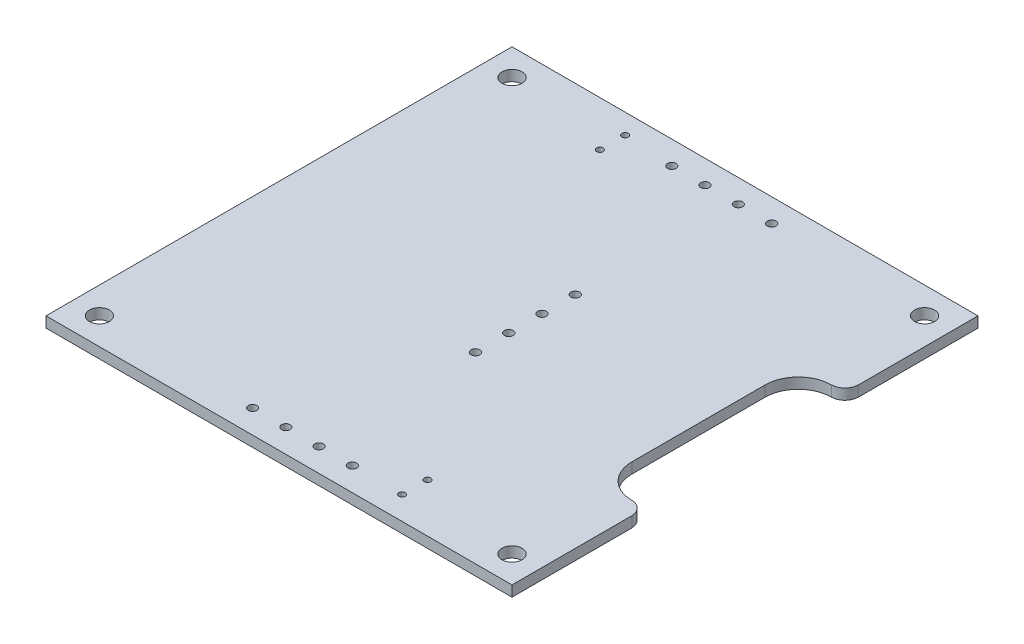
SolidWorks part; units mm, degrees
ref_plane "Front Plane" through (0, 0, 0) normal (0, 0, 1) x (1, 0, 0)
ref_plane "Top Plane" through (0, 0, 0) normal (0, 1, 0) x (1, 0, 0)
ref_plane "Right Plane" through (0, 0, 0) normal (1, 0, 0) x (0, 0, -1)
sketch "Sketch1" plane through (0, 0, 0) normal (0, 1, 0) x (1, 0, 0)
  line L0 (-16.002, 25.9927) -> (-28.0035, 25.9927) construction
  line L1 (-28.0035, 33.9937) -> (-16.002, 33.9937) construction
  line L2 (-16.002, 33.9937) -> (-16.002, 25.9927) construction
  line L3 (15.494, -33.5068) -> (27.4955, -33.5068) construction
  line L4 (27.4955, -33.5068) -> (27.4955, -25.5058) construction
  line L5 (15.494, -25.5058) -> (15.494, -33.5068) construction
  line L6 (-4.4662, 10.8585) -> (8.4667, 10.8585) construction
  line L7 (8.4667, -10.3293) -> (-4.4662, -10.3293) construction
  line L8 (-10.8585, -25.019) -> (-10.8585, -37.973) construction
  line L9 (10.3293, -37.973) -> (10.3293, -25.019) construction
  line L10 (10.8585, 25.019) -> (10.8585, 37.973) construction
  line L11 (10.8585, 37.973) -> (-10.3293, 37.973) construction
  line L12 (-10.3293, 37.973) -> (-10.3293, 25.019) construction
  line L13 (-10.3293, 25.019) -> (10.8585, 25.019) construction
  line L14 (35.0097, 35.0097) -> (-35.0097, 35.0097)
  line L15 (-35.0097, -35.0097) -> (35.0097, -35.0097)
  line L16 (35.0097, -35.0097) -> (35.0097, -16.9968)
  line L17 (35.0097, -16.9968) -> (34.9885, -16.9968)
  line L18 (32.9988, -15.0072) -> (32.9777, -14.986)
  line L19 (28.0035, -9.9907) -> (28.0035, 9.9907)
  line L20 (28.0035, 9.9907) -> (28.0035, 10.0118)
  line L21 (32.9777, 15.0072) -> (32.9988, 15.0283)
  line L22 (34.9885, 17.018) -> (35.0097, 16.9968)
  line L23 (-35.0097, 35.0097) -> (-35.0097, -35.0097)
  line L24 (-4.4662, -10.3293) -> (-4.4662, 10.8585) construction
  line L25 (-10.8585, -25.019) -> (10.3293, -25.019) construction
  line L26 (10.3293, -37.973) -> (-10.8585, -37.973) construction
  line L27 (15.494, -25.5058) -> (27.4955, -25.5058) construction
  line L28 (35.0097, -35.0097) -> (-35.0097, 35.0097) construction
  line L29 (35.0097, 35.0097) -> (-35.0097, -35.0097) construction
  line L30 (-28.0035, 33.9937) -> (-28.0035, 25.9927) construction
  line L31 (-33.9937, 31.0092) -> (-28.0247, 31.0092) construction
  line L32 (-19.304, 30.1202) -> (-10.7103, 30.1202) construction
  line L33 (-8.1492, 31.5172) -> (-6.858, 31.5172) construction
  line L34 (-3.1538, 31.5172) -> (-1.8627, 31.5172) construction
  line L35 (1.8415, 31.5172) -> (3.1327, 31.5172) construction
  line L36 (6.8368, 31.5172) -> (8.1492, 31.5172) construction
  line L37 (28.0035, 31.0092) -> (33.9725, 31.0092) construction
  line L38 (1.3335, 7.5142) -> (2.6458, 7.5142) construction
  line L39 (1.3335, 2.5188) -> (2.6458, 2.5188) construction
  line L40 (1.3335, -2.4765) -> (2.6458, -2.4765) construction
  line L41 (1.3335, -7.493) -> (2.6458, -7.493) construction
  line L42 (-33.9937, -30.988) -> (-28.0247, -30.988) construction
  line L43 (-8.1492, -31.4748) -> (-6.858, -31.4748) construction
  line L44 (-3.1538, -31.4748) -> (-1.8627, -31.4748) construction
  line L45 (1.8415, -31.4748) -> (3.1327, -31.4748) construction
  line L46 (6.8368, -31.4748) -> (8.1492, -31.4748) construction
  line L47 (10.7103, -29.591) -> (19.2828, -29.591) construction
  line L48 (28.0035, -30.988) -> (33.9725, -30.988) construction
  line L49 (-15.494, 32.004) -> (-14.5203, 32.004) construction
  line L50 (-15.494, 28.2152) -> (-14.5203, 28.2152) construction
  line L51 (14.4992, -27.686) -> (15.4728, -27.686) construction
  line L52 (14.4992, -31.496) -> (15.4728, -31.496) construction
  circle A0 centre (-7.5036, 31.5172) radius 0.6456
  circle A1 centre (-2.5083, 31.5172) radius 0.6456
  circle A2 centre (2.4871, 31.5172) radius 0.6456
  circle A3 centre (7.493, 31.5172) radius 0.6562
  circle A4 centre (-15.0072, 28.2152) radius 0.4868
  circle A5 centre (-15.0072, 32.004) radius 0.4868
  circle A6 centre (1.9897, 7.5142) radius 0.6562
  circle A7 centre (1.9897, 2.5188) radius 0.6562
  circle A8 centre (1.9897, -2.4765) radius 0.6562
  circle A9 centre (1.9897, -7.493) radius 0.6562
  circle A10 centre (-7.5036, -31.4748) radius 0.6456
  circle A11 centre (-2.5083, -31.4748) radius 0.6456
  circle A12 centre (2.4871, -31.4748) radius 0.6456
  circle A13 centre (7.493, -31.4748) radius 0.6562
  circle A14 centre (-31.0092, 31.0092) radius 1.5
  circle A15 centre (30.988, 31.0092) radius 1.5
  circle A16 centre (-31.0092, -30.988) radius 1.5
  circle A17 centre (30.988, -30.988) radius 1.5
  circle A18 centre (14.986, -27.686) radius 0.4868
  circle A19 centre (14.986, -31.496) radius 0.4868
  spline S2 degree 3 poles (14.4992, -31.496) (14.4992, -31.75) (14.7108, -31.9828) (14.986, -31.9828) (15.24, -31.9828) (15.4728, -31.75) (15.4728, -31.496) knots 2 2 2 2 3 3 3 4 4 4 4 construction
  spline S3 degree 3 poles (15.4728, -31.496) (15.4728, -31.2208) (15.24, -31.0092) (14.986, -31.0092) (14.7108, -31.0092) (14.4992, -31.2208) (14.4992, -31.496) knots 0 0 0 0 1 1 1 2 2 2 2 construction
  spline S4 degree 3 poles (14.4992, -27.686) (14.4992, -27.94) (14.7108, -28.1728) (14.986, -28.1728) (15.24, -28.1728) (15.4728, -27.94) (15.4728, -27.686) knots 2 2 2 2 3 3 3 4 4 4 4 construction
  spline S5 degree 3 poles (15.4728, -27.686) (15.4728, -27.4108) (15.24, -27.1992) (14.986, -27.1992) (14.7108, -27.1992) (14.4992, -27.4108) (14.4992, -27.686) knots 0 0 0 0 1 1 1 2 2 2 2 construction
  spline S6 degree 3 poles (10.7103, -29.591) (10.7103, -31.9617) (12.6153, -33.8878) (14.986, -33.8878) (17.3567, -33.8878) (19.2828, -31.9617) (19.2828, -29.591) knots 2 2 2 2 3 3 3 4 4 4 4 construction
  spline S7 degree 3 poles (19.2828, -29.591) (19.2828, -27.1992) (17.3567, -25.2942) (14.986, -25.2942) (12.6153, -25.2942) (10.7103, -27.1992) (10.7103, -29.591) knots 0 0 0 0 1 1 1 2 2 2 2 construction
  spline S8 degree 3 poles (-15.494, 32.004) (-15.494, 31.75) (-15.2823, 31.5172) (-15.0072, 31.5172) (-14.7532, 31.5172) (-14.5203, 31.75) (-14.5203, 32.004) knots 2 2 2 2 3 3 3 4 4 4 4 construction
  spline S9 degree 3 poles (-14.5203, 32.004) (-14.5203, 32.2792) (-14.7532, 32.4908) (-15.0072, 32.4908) (-15.2823, 32.4908) (-15.494, 32.2792) (-15.494, 32.004) knots 0 0 0 0 1 1 1 2 2 2 2 construction
  spline S10 degree 3 poles (-15.494, 28.2152) (-15.494, 27.9612) (-15.2823, 27.7283) (-15.0072, 27.7283) (-14.7532, 27.7283) (-14.5203, 27.9612) (-14.5203, 28.2152) knots 2 2 2 2 3 3 3 4 4 4 4 construction
  spline S11 degree 3 poles (-14.5203, 28.2152) (-14.5203, 28.4903) (-14.7532, 28.702) (-15.0072, 28.702) (-15.2823, 28.702) (-15.494, 28.4903) (-15.494, 28.2152) knots 0 0 0 0 1 1 1 2 2 2 2 construction
  spline S12 degree 3 poles (-19.304, 30.1202) (-19.304, 27.7495) (-17.399, 25.8233) (-15.0072, 25.8233) (-12.6365, 25.8233) (-10.7103, 27.7495) (-10.7103, 30.1202) knots 2 2 2 2 3 3 3 4 4 4 4 construction
  spline S13 degree 3 poles (-10.7103, 30.1202) (-10.7103, 32.4908) (-12.6365, 34.3958) (-15.0072, 34.3958) (-17.399, 34.3958) (-19.304, 32.4908) (-19.304, 30.1202) knots 0 0 0 0 1 1 1 2 2 2 2 construction
  spline S14 degree 3 poles (1.3335, -7.493) (1.3335, -7.8528) (1.6087, -8.1492) (1.9897, -8.1492) (2.3495, -8.1492) (2.6458, -7.8528) (2.6458, -7.493) knots 2 2 2 2 3 3 3 4 4 4 4 construction
  spline S15 degree 3 poles (2.6458, -7.493) (2.6458, -7.112) (2.3495, -6.8368) (1.9897, -6.8368) (1.6087, -6.8368) (1.3335, -7.112) (1.3335, -7.493) knots 0 0 0 0 1 1 1 2 2 2 2 construction
  spline S16 degree 3 poles (1.3335, -2.4765) (1.3335, -2.8363) (1.6087, -3.1327) (1.9897, -3.1327) (2.3495, -3.1327) (2.6458, -2.8363) (2.6458, -2.4765) knots 2 2 2 2 3 3 3 4 4 4 4 construction
  spline S17 degree 3 poles (2.6458, -2.4765) (2.6458, -2.1167) (2.3495, -1.8415) (1.9897, -1.8415) (1.6087, -1.8415) (1.3335, -2.1167) (1.3335, -2.4765) knots 0 0 0 0 1 1 1 2 2 2 2 construction
  spline S18 degree 3 poles (1.3335, 7.5142) (1.3335, 7.1543) (1.6087, 6.858) (1.9897, 6.858) (2.3495, 6.858) (2.6458, 7.1543) (2.6458, 7.5142) knots 2 2 2 2 3 3 3 4 4 4 4 construction
  spline S19 degree 3 poles (2.6458, 7.5142) (2.6458, 7.874) (2.3495, 8.1492) (1.9897, 8.1492) (1.6087, 8.1492) (1.3335, 7.874) (1.3335, 7.5142) knots 0 0 0 0 1 1 1 2 2 2 2 construction
  spline S20 degree 3 poles (1.3335, 2.5188) (1.3335, 2.159) (1.6087, 1.8627) (1.9897, 1.8627) (2.3495, 1.8627) (2.6458, 2.159) (2.6458, 2.5188) knots 2 2 2 2 3 3 3 4 4 4 4 construction
  spline S21 degree 3 poles (2.6458, 2.5188) (2.6458, 2.8787) (2.3495, 3.1538) (1.9897, 3.1538) (1.6087, 3.1538) (1.3335, 2.8787) (1.3335, 2.5188) knots 0 0 0 0 1 1 1 2 2 2 2 construction
  spline S22 degree 3 poles (6.8368, -31.4748) (6.8368, -31.8347) (7.112, -32.131) (7.493, -32.131) (7.8528, -32.131) (8.1492, -31.8347) (8.1492, -31.4748) knots 2 2 2 2 3 3 3 4 4 4 4 construction
  spline S23 degree 3 poles (8.1492, -31.4748) (8.1492, -31.115) (7.8528, -30.8398) (7.493, -30.8398) (7.112, -30.8398) (6.8368, -31.115) (6.8368, -31.4748) knots 0 0 0 0 1 1 1 2 2 2 2 construction
  spline S24 degree 3 poles (1.8415, -31.4748) (1.8415, -31.8347) (2.1167, -32.131) (2.4765, -32.131) (2.8363, -32.131) (3.1327, -31.8347) (3.1327, -31.4748) knots 2 2 2 2 3 3 3 4 4 4 4 construction
  spline S25 degree 3 poles (3.1327, -31.4748) (3.1327, -31.115) (2.8363, -30.8398) (2.4765, -30.8398) (2.1167, -30.8398) (1.8415, -31.115) (1.8415, -31.4748) knots 0 0 0 0 1 1 1 2 2 2 2 construction
  spline S26 degree 3 poles (-8.1492, -31.4748) (-8.1492, -31.8347) (-7.874, -32.131) (-7.5142, -32.131) (-7.1543, -32.131) (-6.858, -31.8347) (-6.858, -31.4748) knots 2 2 2 2 3 3 3 4 4 4 4 construction
  spline S27 degree 3 poles (-6.858, -31.4748) (-6.858, -31.115) (-7.1543, -30.8398) (-7.5142, -30.8398) (-7.874, -30.8398) (-8.1492, -31.115) (-8.1492, -31.4748) knots 0 0 0 0 1 1 1 2 2 2 2 construction
  spline S28 degree 3 poles (-3.1538, -31.4748) (-3.1538, -31.8347) (-2.8787, -32.131) (-2.5188, -32.131) (-2.159, -32.131) (-1.8627, -31.8347) (-1.8627, -31.4748) knots 2 2 2 2 3 3 3 4 4 4 4 construction
  spline S29 degree 3 poles (-1.8627, -31.4748) (-1.8627, -31.115) (-2.159, -30.8398) (-2.5188, -30.8398) (-2.8787, -30.8398) (-3.1538, -31.115) (-3.1538, -31.4748) knots 0 0 0 0 1 1 1 2 2 2 2 construction
  spline S30 degree 3 poles (-8.1492, 31.5172) (-8.1492, 31.1573) (-7.874, 30.861) (-7.5142, 30.861) (-7.1543, 30.861) (-6.858, 31.1573) (-6.858, 31.5172) knots 2 2 2 2 3 3 3 4 4 4 4 construction
  spline S31 degree 3 poles (-6.858, 31.5172) (-6.858, 31.877) (-7.1543, 32.1522) (-7.5142, 32.1522) (-7.874, 32.1522) (-8.1492, 31.877) (-8.1492, 31.5172) knots 0 0 0 0 1 1 1 2 2 2 2 construction
  spline S32 degree 3 poles (-3.1538, 31.5172) (-3.1538, 31.1573) (-2.8787, 30.861) (-2.5188, 30.861) (-2.159, 30.861) (-1.8627, 31.1573) (-1.8627, 31.5172) knots 2 2 2 2 3 3 3 4 4 4 4 construction
  spline S33 degree 3 poles (-1.8627, 31.5172) (-1.8627, 31.877) (-2.159, 32.1522) (-2.5188, 32.1522) (-2.8787, 32.1522) (-3.1538, 31.877) (-3.1538, 31.5172) knots 0 0 0 0 1 1 1 2 2 2 2 construction
  spline S34 degree 3 poles (6.8368, 31.5172) (6.8368, 31.1573) (7.112, 30.861) (7.493, 30.861) (7.8528, 30.861) (8.1492, 31.1573) (8.1492, 31.5172) knots 2 2 2 2 3 3 3 4 4 4 4 construction
  spline S35 degree 3 poles (8.1492, 31.5172) (8.1492, 31.877) (7.8528, 32.1522) (7.493, 32.1522) (7.112, 32.1522) (6.8368, 31.877) (6.8368, 31.5172) knots 0 0 0 0 1 1 1 2 2 2 2 construction
  spline S36 degree 3 poles (1.8415, 31.5172) (1.8415, 31.1573) (2.1167, 30.861) (2.4765, 30.861) (2.8363, 30.861) (3.1327, 31.1573) (3.1327, 31.5172) knots 2 2 2 2 3 3 3 4 4 4 4 construction
  spline S37 degree 3 poles (3.1327, 31.5172) (3.1327, 31.877) (2.8363, 32.1522) (2.4765, 32.1522) (2.1167, 32.1522) (1.8415, 31.877) (1.8415, 31.5172) knots 0 0 0 0 1 1 1 2 2 2 2 construction
  spline S38 degree 2 poles (8.4667, 10.8585) (8.4667, 10.8585) (8.4667, -10.3293) knots 1 1 1 2 2 2 construction
  spline S42 degree 3 poles (28.0035, -30.988) (28.0035, -32.6178) (29.337, -33.9725) (30.988, -33.9725) (32.6178, -33.9725) (33.9725, -32.6178) (33.9725, -30.988) knots 2 2 2 2 3 3 3 4 4 4 4 construction
  spline S43 degree 3 poles (33.9725, -30.988) (33.9725, -29.337) (32.6178, -28.0035) (30.988, -28.0035) (29.337, -28.0035) (28.0035, -29.337) (28.0035, -30.988) knots 0 0 0 0 1 1 1 2 2 2 2 construction
  spline S44 degree 3 poles (-33.9937, -30.988) (-33.9937, -32.6178) (-32.6602, -33.9725) (-31.0092, -33.9725) (-29.3793, -33.9725) (-28.0247, -32.6178) (-28.0247, -30.988) knots 2 2 2 2 3 3 3 4 4 4 4 construction
  spline S45 degree 3 poles (-28.0247, -30.988) (-28.0247, -29.337) (-29.3793, -28.0035) (-31.0092, -28.0035) (-32.6602, -28.0035) (-33.9937, -29.337) (-33.9937, -30.988) knots 0 0 0 0 1 1 1 2 2 2 2 construction
  spline S46 degree 3 poles (-33.9937, 31.0092) (-33.9937, 29.3793) (-32.6602, 28.0247) (-31.0092, 28.0247) (-29.3793, 28.0247) (-28.0247, 29.3793) (-28.0247, 31.0092) knots 2 2 2 2 3 3 3 4 4 4 4 construction
  spline S47 degree 3 poles (-28.0247, 31.0092) (-28.0247, 32.6602) (-29.3793, 33.9937) (-31.0092, 33.9937) (-32.6602, 33.9937) (-33.9937, 32.6602) (-33.9937, 31.0092) knots 0 0 0 0 1 1 1 2 2 2 2 construction
  spline S48 degree 3 poles (28.0035, 31.0092) (28.0035, 29.3793) (29.337, 28.0247) (30.988, 28.0247) (32.6178, 28.0247) (33.9725, 29.3793) (33.9725, 31.0092) knots 2 2 2 2 3 3 3 4 4 4 4 construction
  spline S49 degree 3 poles (33.9725, 31.0092) (33.9725, 32.6602) (32.6178, 33.9937) (30.988, 33.9937) (29.337, 33.9937) (28.0035, 32.6602) (28.0035, 31.0092) knots 0 0 0 0 1 1 1 2 2 2 2 construction
  spline S50 degree 2 poles (35.0097, 16.9968) (35.0097, 35.0097) (35.0097, 35.0097) knots 0 0 0 1 1 1
  spline S52 degree 3 poles (34.9885, -16.9968) (34.9885, -15.8962) (34.0783, -15.0072) (32.9988, -15.0072) knots 6 6 6 6 7 7 7 7
  spline S53 degree 3 poles (32.9777, -14.986) (30.226, -14.986) (28.0035, -12.7423) (28.0035, -9.9907) knots 8 8 8 8 9 9 9 9
  spline S54 degree 3 poles (28.0035, 10.0118) (28.0035, 12.7847) (30.226, 15.0072) (32.9777, 15.0072) knots 11 11 11 11 12 12 12 12
  spline S55 degree 3 poles (32.9988, 15.0283) (34.0783, 15.0283) (34.9885, 15.9385) (34.9885, 17.018) knots 13 13 13 13 14 14 14 14
  point P0 (0, 0)
  dimension "D1" = 70.0193
  dimension "D2" = 3
extrude "Boss-Extrude1" add sketch "Sketch1" along normal blind 1.6 contours L21 S55 L22 S50 L14 L23 L15 L16 L17 S52 L18 S53 L19 L20 S54 A0 A1 A2 A3 A4 A5 A6 A7 A8 A9 A10 A11 A12 A13 A14 A15 A16 A17 | A18 | A19
